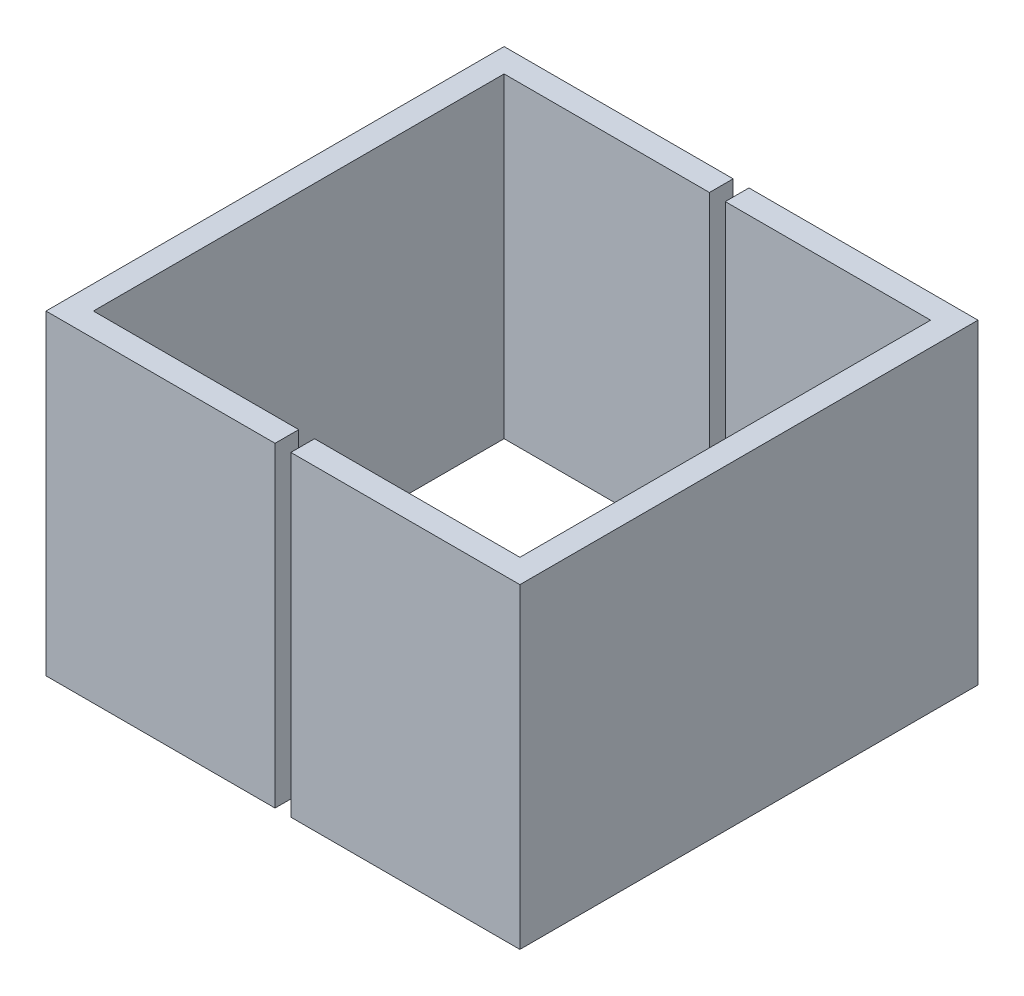
SolidWorks part; units mm, degrees
ref_plane "Front Plane" through (0, 0, 0) normal (0, 0, 1) x (1, 0, 0)
ref_plane "Top Plane" through (0, 0, 0) normal (0, 1, 0) x (1, 0, 0)
ref_plane "Right Plane" through (0, 0, 0) normal (1, 0, 0) x (0, 0, -1)
sketch "Sketch1" plane through (0, 0, 0) normal (0, 1, 0) x (1, 0, 0)
  line L0 (13.5, 13) -> (-13.5, 13)
  line L1 (15, -14.5) -> (-15, -14.5)
  line L2 (15, -14.5) -> (15, 14.5)
  line L3 (15, 14.5) -> (-15, 14.5)
  line L4 (-15, -14.5) -> (-15, 14.5)
  line L5 (15, -14.5) -> (-15, 14.5) construction
  line L6 (15, 14.5) -> (-15, -14.5) construction
  line L7 (-13.5, -13) -> (-13.5, 13)
  line L8 (13.5, -13) -> (-13.5, -13)
  line L9 (13.5, -13) -> (13.5, 13)
  point P0 (0, 0)
  dimension "D1" = 26
  dimension "D3" = 27
  dimension "D2" = 1.5
extrude "Boss-Extrude1" add sketch "Sketch1" along normal blind 20
sketch "Sketch2" plane through (0, 20, 0) normal (0, 1, 0) x (1, 0, 0)
  line L0 (-15, -14.5) -> (15, -14.5) construction
  line L1 (0.5, 14.5) -> (-0.5, 14.5)
  line L2 (0.5, 14.5) -> (0.5, -14.5)
  line L3 (0.5, -14.5) -> (-0.5, -14.5)
  line L4 (-0.5, 14.5) -> (-0.5, -14.5)
  line L5 (0.5, 14.5) -> (-0.5, -14.5) construction
  line L6 (0.5, -14.5) -> (-0.5, 14.5) construction
  point P0 (0, 0)
  dimension "D1" = 1
extrude "Cut-Extrude1" cut sketch "Sketch2" against normal through all
